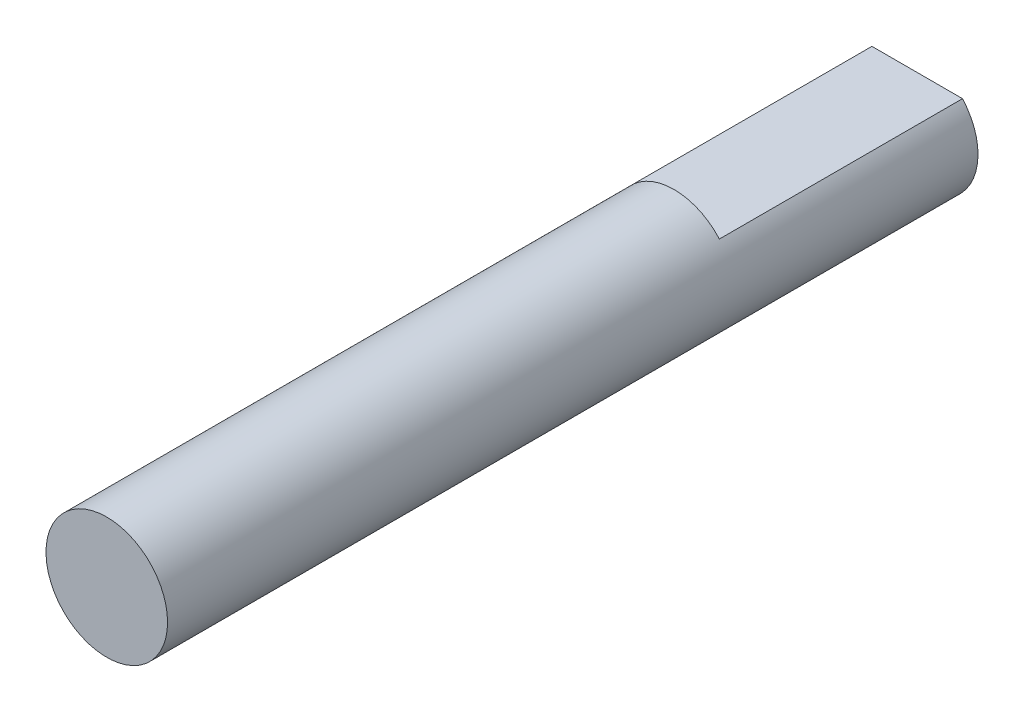
SolidWorks part; units mm, degrees
ref_plane "Front Plane" through (0, 0, 0) normal (0, 0, 1) x (1, 0, 0)
ref_plane "Top Plane" through (0, 0, 0) normal (0, 1, 0) x (1, 0, 0)
ref_plane "Right Plane" through (0, 0, 0) normal (1, 0, 0) x (0, 0, -1)
sketch "Sketch1" plane through (0, 0, 0) normal (0, 0, 1) x (1, 0, 0)
  line L1 (2.2361, 2) -> (-2.2361, 2)
  arc A0 (-2.2361, 2) -> (2.2361, 2) centre (0, 0) ccw
  dimension "D1" = 6
  dimension "D2" = 2
extrude "Boss-Extrude1" add sketch "Sketch1" along normal blind 40
sketch "Sketch2" plane through (0, 0, 40) normal (0, 0, 1) x (1, 0, 0)
  line L0 (-2.2361, 2) -> (2.2361, 2)
  arc A0 (2.2361, 2) -> (-2.2361, 2) centre (0, 0) ccw
extrude "Boss-Extrude2" add sketch "Sketch2" against normal blind 28
